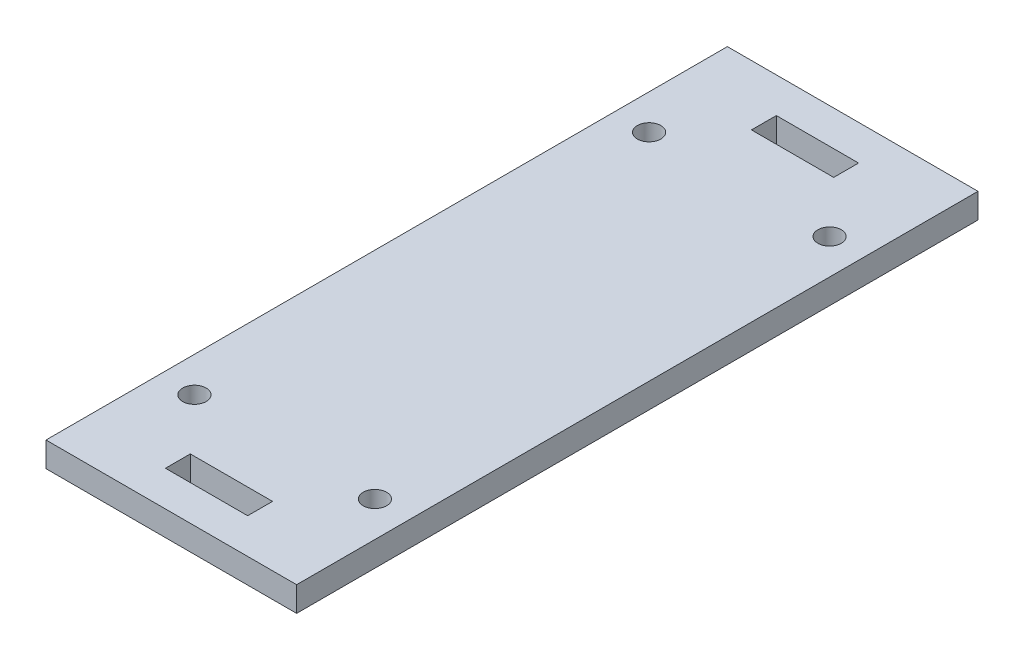
SolidWorks part; units mm, degrees
ref_plane "Front Plane" through (0, 0, 0) normal (0, 0, 1) x (1, 0, 0)
ref_plane "Top Plane" through (0, 0, 0) normal (0, 1, 0) x (1, 0, 0)
ref_plane "Right Plane" through (0, 0, 0) normal (1, 0, 0) x (0, 0, -1)
sketch "Sketch1" plane through (0, 0, 0) normal (0, 1, 0) x (1, 0, 0)
  line L1 (0, 0) -> (32, 0)
  line L2 (0, 0) -> (0, 87)
  line L3 (0, 87) -> (32, 87)
  line L4 (32, 0) -> (32, 87)
  line L5 (10.75, 7.675) -> (21.25, 7.675)
  line L6 (10.75, 7.675) -> (10.75, 4.5)
  line L7 (10.75, 4.5) -> (21.25, 4.5)
  line L8 (21.25, 7.675) -> (21.25, 4.5)
  line L9 (10.75, 82.5) -> (21.25, 82.5)
  line L10 (10.75, 82.5) -> (10.75, 79.325)
  line L11 (10.75, 79.325) -> (21.25, 79.325)
  line L12 (21.25, 82.5) -> (21.25, 79.325)
  circle A0 centre (4.475, 72.525) radius 1.5
  circle A1 centre (27.525, 72.525) radius 1.5
  circle A2 centre (27.525, 14.475) radius 1.5
  circle A3 centre (4.475, 14.475) radius 1.5
  point P17 (16, 4.5)
  point P18 (16, 0)
  dimension "D5" = 3
  dimension "D1" = 32
  dimension "D2" = 87
  dimension "D3" = 23.05
  dimension "D4" = 58.05
  dimension "D6" = 4.475
  dimension "D7" = 14.475
  dimension "D8" = 3.175
  dimension "D9" = 10.5
  dimension "D10" = 4.5
  dimension "D11" = 4.5
extrude "Boss-Extrude1" add sketch "Sketch1" along normal blind 3.175
